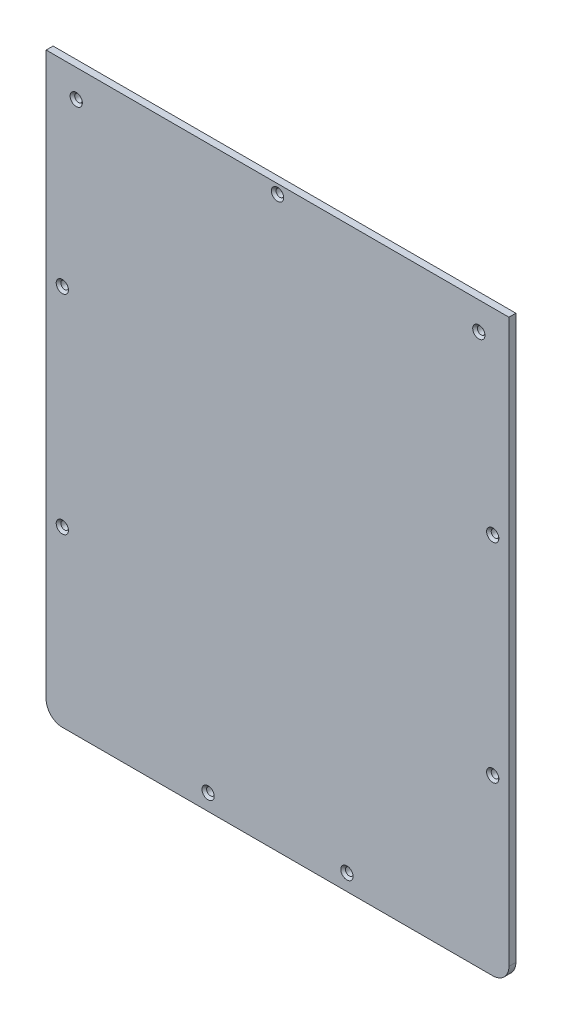
SolidWorks part; units mm, degrees
ref_plane "Front" through (0, 0, 0) normal (0, 0, 1) x (1, 0, 0)
ref_plane "Top" through (0, 0, 0) normal (0, 1, 0) x (1, 0, 0)
ref_plane "Right" through (0, 0, 0) normal (1, 0, 0) x (0, 0, -1)
sketch "Sketch1" plane through (0, 0, 0) normal (0, 0, 1) x (1, 0, 0)
  line L0 (200, 250) -> (200, 7) construction
  line L1 (0, 0) -> (200, 0)
  line L2 (0, 0) -> (0, 250)
  line L3 (0, 250) -> (200, 250)
  line L4 (200, 0) -> (200, 250)
  line L5 (195, 250) -> (200, 250) construction
extrude "Boss-Extrude1" add sketch "Sketch1" along normal blind 3
fillet "Fillet1" radius 7 2 edges at (200, 0, 1.5) (0, 0, 1.5)
sketch "Sketch2" plane through (0, 0, 0) normal (0, 0, 1) x (1, 0, 0)
  circle A0 centre (70, 7) radius 1.65
  circle A1 centre (7, 75) radius 1.65
  circle A2 centre (193, 75) radius 1.65
  circle A3 centre (13, 238) radius 1.65
  circle A4 centre (100, 246) radius 1.65
  circle A5 centre (187, 238) radius 1.65
  circle A6 centre (7, 75) radius 1.25 construction
  circle A7 centre (70, 7) radius 1.25 construction
  circle A8 centre (193, 75) radius 1.25 construction
  circle A9 centre (187, 238) radius 1.25 construction
  circle A10 centre (100, 246) radius 1.25 construction
  circle A11 centre (13, 238) radius 1.25 construction
  circle A12 centre (7, 165) radius 1.65
  circle A13 centre (7, 165) radius 1.25 construction
  circle A14 centre (193, 165) radius 1.65
  circle A15 centre (193, 165) radius 1.25 construction
  circle A16 centre (130, 7) radius 1.65
  dimension "D1" = 3.3
extrude "Cut-Extrude2" cut sketch "Sketch2" along normal through all
chamfer "Chamfer1" distance 1 angle 45 9 edges at (188.65, 238, 3) (101.65, 246, 3) (14.65, 238, 3) (194.65, 165, 3) (8.65, 165, 3) (194.65, 75, 3) (8.65, 75, 3) (131.65, 7, 3) (71.65, 7, 3)
